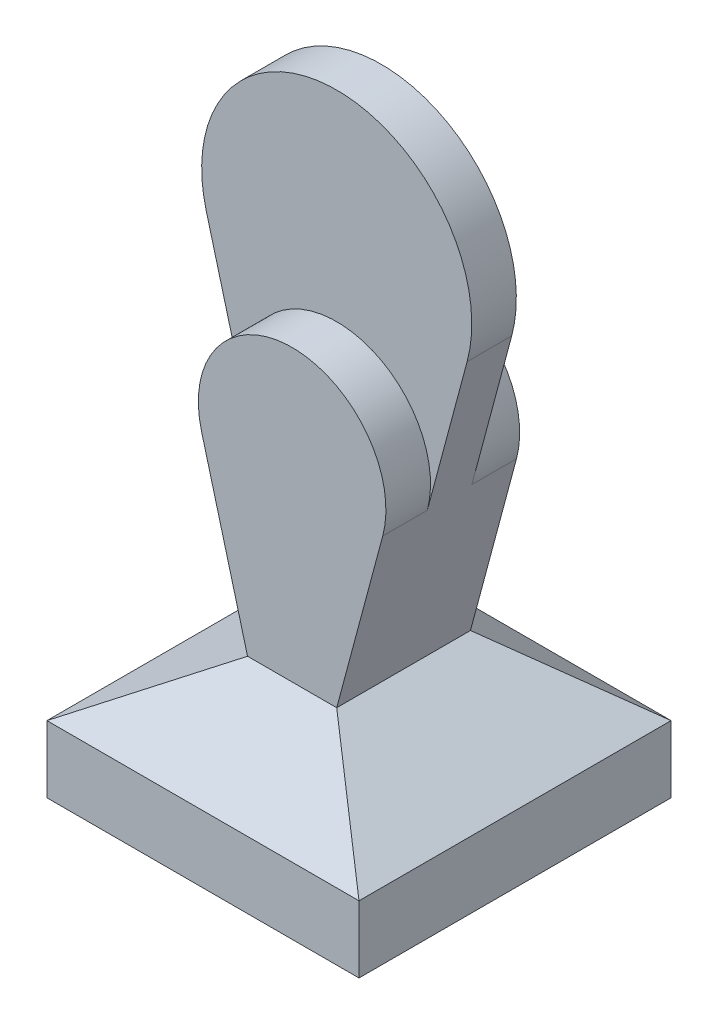
SolidWorks part; units mm, degrees
ref_plane "Front" through (0, 0, 0) normal (0, 0, 1) x (1, 0, 0)
ref_plane "Top" through (0, 0, 0) normal (0, 1, 0) x (1, 0, 0)
ref_plane "Right" through (0, 0, 0) normal (1, 0, 0) x (0, 0, -1)
sketch "Sketch1" plane through (0, 0, 0) normal (0, 1, 0) x (1, 0, 0)
  line L0 (35, 35) -> (-35, -35) construction
  line L1 (-35, 35) -> (35, 35)
  line L2 (-35, 35) -> (-35, -35)
  line L3 (-35, -35) -> (35, -35)
  line L4 (35, 35) -> (35, -35)
  dimension "D1" = 70
extrude "Extrude1" add sketch "Sketch1" along normal blind 15
sketch "Sketch2" plane through (0, 15, 0) normal (0, 1, 0) x (-1, 0, 0)
  line L1 (35, -35) -> (-35, -35)
  line L2 (35, -35) -> (35, 35)
  line L3 (35, 35) -> (-35, 35)
  line L4 (-35, -35) -> (-35, 35)
ref_plane "Plane1" through (0, 30, 0) normal (0, 1, 0) x (-1, 0, 0)
sketch "Sketch3" plane through (0, 30, 0) normal (0, 1, 0) x (-1, 0, 0)
  line L0 (10, 15) -> (-10, -15) construction
  line L1 (-10, 15) -> (10, 15)
  line L2 (-10, 15) -> (-10, -15)
  line L3 (-10, -15) -> (10, -15)
  line L4 (10, 15) -> (10, -15)
  dimension "D1" = 30
  dimension "D2" = 20
loft "Loft1" add profiles "Sketch2", "Sketch3"
sketch "Sketch4" plane through (0, 0, 0) normal (0, 0, 1) x (1, 0, 0)
  line L0 (10, 30) -> (29.2577, 101.8706)
  line L1 (-10, 30) -> (-29.2577, 101.8706)
  line L2 (34.9791, 30) -> (-44.327, 30) construction
  line L3 (0, 0) -> (0, 140) construction
  line L4 (-10, 30) -> (10, 30)
  arc A0 (29.2577, 101.8706) -> (-29.2577, 101.8706) centre (0, 109.7102) ccw
  dimension "D1" = 75
  dimension "D2" = 75
  dimension "D3" = 140
extrude "Extrude2" add sketch "Sketch4" along normal mid plane 10
sketch "Sketch5" plane through (0, 0, 0) normal (0, 0, 1) x (1, 0, 0)
  line L0 (10, 30) -> (29.2577, 101.8706) construction
  line L1 (0, 0) -> (0, 95) construction
  line L2 (20.3207, 68.5175) -> (10, 30)
  line L3 (10, 30) -> (-10, 30)
  line L4 (-10, 30) -> (-20.3207, 68.5175)
  arc A0 (20.3207, 68.5175) -> (-20.3207, 68.5175) centre (0, 73.9624) ccw
  dimension "D1" = 95
extrude "Extrude3" add sketch "Sketch5" along normal mid plane 30
